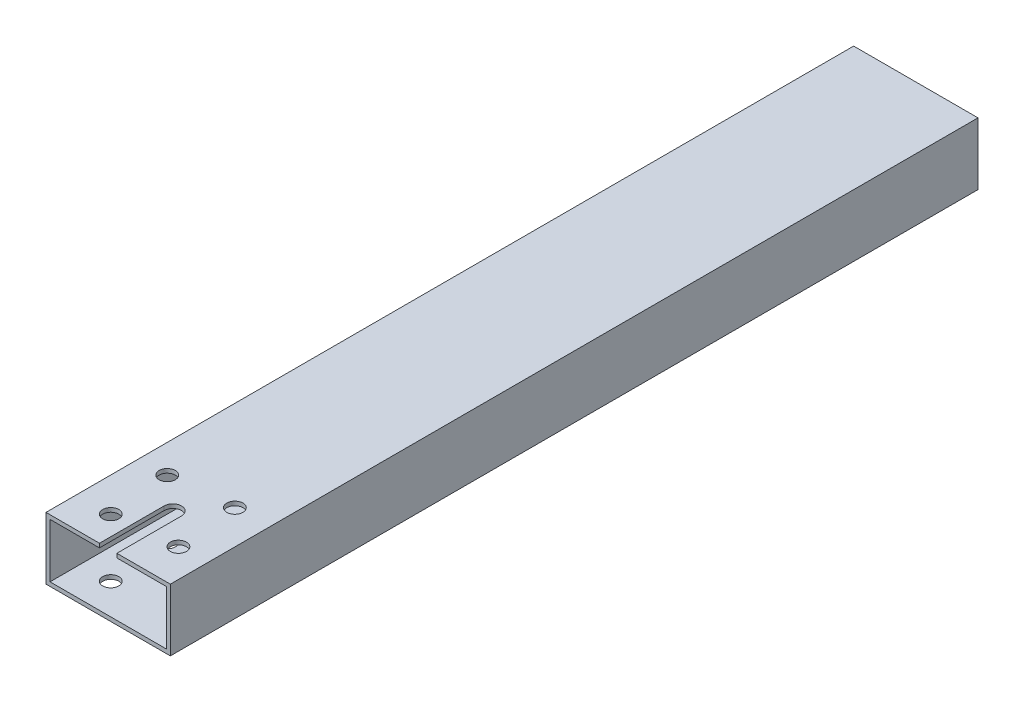
SolidWorks part; units mm, degrees
material "6061-O (SS)"
ref_plane "Front Plane" through (0, 0, 0) normal (0, 0, 1) x (1, 0, 0)
ref_plane "Top Plane" through (0, 0, 0) normal (0, 1, 0) x (1, 0, 0)
ref_plane "Right Plane" through (0, 0, 0) normal (1, 0, 0) x (0, 0, -1)
sketch "Sketch1" plane through (0, 0, 0) normal (0, 0, 1) x (1, 0, 0)
  line L1 (-14.0056, 17.5664) -> (36.7944, 17.5664)
  line L2 (-14.0056, 17.5664) -> (-14.0056, -7.8336)
  line L3 (-14.0056, -7.8336) -> (36.7944, -7.8336)
  line L4 (36.7944, 17.5664) -> (36.7944, -7.8336)
  line L5 (-12.3546, 15.9154) -> (35.1434, 15.9154)
  line L6 (-12.3546, 15.9154) -> (-12.3546, -6.1826)
  line L7 (-12.3546, -6.1826) -> (35.1434, -6.1826)
  line L8 (35.1434, 15.9154) -> (35.1434, -6.1826)
  dimension "D1" = 25.4
  dimension "D2" = 50.8
  dimension "D3" = 1.651
  dimension "D4" = 1.651
  dimension "D5" = 1.651
  dimension "D6" = 1.651
extrude "Boss-Extrude1" add sketch "Sketch1" along normal blind 330
sketch "Sketch2" plane through (0, 17.5664, 0) normal (0, 1, 0) x (1, 0, 0)
  line L0 (7.8384, -303.584) -> (7.8384, -330)
  line L1 (14.9504, -303.584) -> (14.9504, -330)
  line L2 (7.8384, -330) -> (14.9504, -330)
  line L3 (36.7944, -330) -> (-14.0056, -330) construction
  line L4 (36.7944, -330) -> (36.7944, 0) construction
  arc A0 (14.9504, -303.584) -> (7.8384, -303.584) centre (11.3944, -303.584) ccw
  circle A1 centre (11.3944, -303.584) radius 18
  circle A2 centre (-2.4233, -292.0484) radius 3.3
  circle A3 centre (22.93, -289.7663) radius 3.3
  circle A4 centre (25.2121, -315.1196) radius 3.3
  circle A5 centre (-0.1412, -317.4017) radius 3.3
  point P12 (0, 0)
  point P13 (0, 0)
  point P14 (0, 0)
  point P21 (11.3944, -303.584)
  point P22 (0, 0)
  dimension "D3" = 36
  dimension "D4" = 6.6
  dimension "D1" = 0
  dimension "D2" = 25.4
  dimension "D5" = 4
extrude "Cut-Extrude2" cut sketch "Sketch2" against normal through all contours A1 A2 | A1 A2 | A1 A3 | A1 A3 | A1 A4 | A1 A4 | A1 A5 | A1 A5
sketch "Sketch4" plane through (0, 17.5664, 0) normal (0, 1, 0) x (1, 0, 0)
  line L0 (7.8384, -303.584) -> (7.8384, -330)
  line L1 (14.9504, -303.584) -> (14.9504, -330)
  line L2 (7.8384, -330) -> (14.9504, -330)
  line L5 (36.7944, -330) -> (-14.0056, -330) construction
  line L6 (36.7944, -330) -> (36.7944, 0) construction
  arc A0 (14.9504, -303.584) -> (7.8384, -303.584) centre (11.3944, -303.584) ccw
  circle A1 centre (11.3944, -303.584) radius 18
  circle A2 centre (-2.4233, -292.0484) radius 3.3
  circle A3 centre (17.5206, -281.2268) radius 3.3
  circle A4 centre (28.3421, -301.1708) radius 3.3
  circle A5 centre (8.3982, -311.9923) radius 3.3
  point P12 (-5.4094, 8.5394)
  point P13 (-5.4094, 8.5394)
  point P14 (-5.4094, 8.5394)
  point P21 (12.9594, -296.6096)
  point P22 (-5.4094, 8.5394)
  line M18 (-14.0056, -330) -> (36.7944, -330)
  dimension "D3" = 36
  dimension "D4" = 6.6
  dimension "D1" = 0
  dimension "D2" = 25.4
  dimension "D5" = 4
extrude "Cut-Extrude3" cut sketch "Sketch4" against normal blind 8.89 contours A5 L0 A1 L1 A0 | L0 A5 | A1 L0 L1 M18
